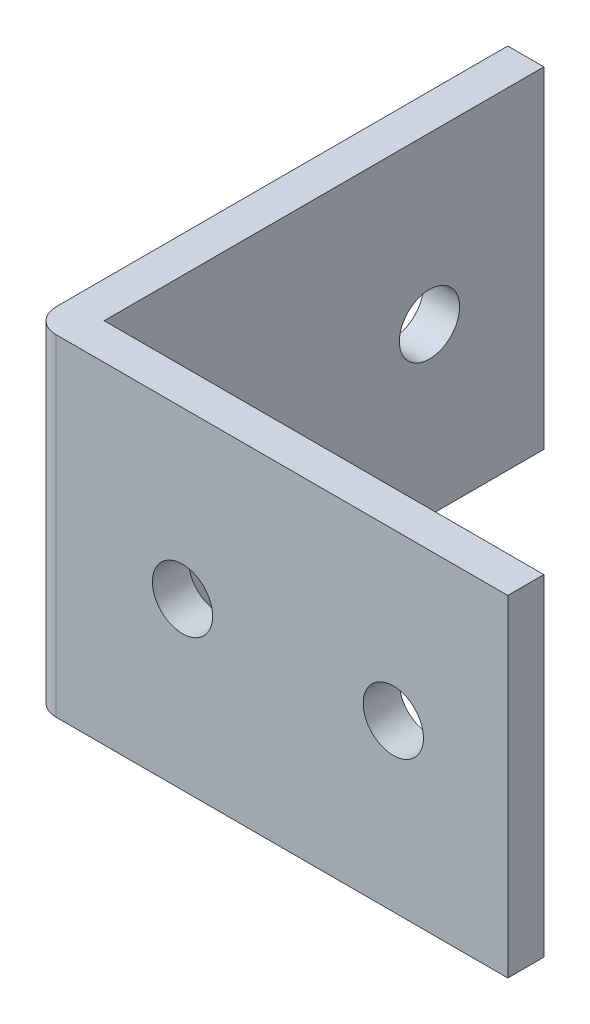
SolidWorks part; units mm, degrees
material "Stainless Steel (ferritic)"
ref_plane "Front Plane" through (0, 0, 0) normal (0, 0, 1) x (1, 0, 0)
ref_plane "Top Plane" through (0, 0, 0) normal (0, 1, 0) x (1, 0, 0)
ref_plane "Right Plane" through (0, 0, 0) normal (1, 0, 0) x (0, 0, -1)
sketch "Sketch1" plane through (0, 0, 0) normal (0, 0, 1) x (1, 0, 0)
  line L1 (-37.1328, 0.8528) -> (2.3672, 0.8528)
  line L2 (-37.1328, 0.8528) -> (-37.1328, -26.6472)
  line L3 (-37.1328, -26.6472) -> (2.3672, -26.6472)
  line L4 (2.3672, 0.8528) -> (2.3672, -26.6472)
  circle A0 centre (-24.6328, -12.8972) radius 2.5
  circle A1 centre (-7.1328, -12.8972) radius 2.5
  point P9 (2.3672, -12.8972)
  point P11 (-37.1328, -12.8972)
  dimension "D2" = 5
  dimension "D3" = 5
  dimension "D1" = 39.5
  dimension "D4" = 17.5
  dimension "D5" = 9.5
  dimension "D6" = 27.5
extrude "Boss-Extrude1" add sketch "Sketch1" along normal blind 3
sketch "Sketch3" plane through (0, 0, 0) normal (0, 0, -1) x (-1, 0, 0)
  line L0 (37.1328, -26.6472) -> (-2.3672, -26.6472) construction
  line L1 (37.1328, 0.8528) -> (34.1328, 0.8528)
  line L2 (37.1328, 0.8528) -> (37.1328, -26.6472)
  line L3 (37.1328, -26.6472) -> (34.1328, -26.6472)
  line L4 (34.1328, 0.8528) -> (34.1328, -26.6472)
  dimension "D1" = 3
extrude "Boss-Extrude2" add sketch "Sketch3" along normal blind 36.5
sketch "Sketch4" plane through (-34.1328, 0, 0) normal (1, 0, 0) x (0, 0, -1)
  line L1 (36.5, 0.8528) -> (36.5, -26.6472) construction
  circle A0 centre (9.5, -12.8972) radius 2.5
  circle A1 centre (27, -12.8972) radius 2.5
  point P8 (36.5, -12.8972)
  dimension "D3" = 5
  dimension "D1" = 17.5
  dimension "D2" = 9.5
extrude "Cut-Extrude1" cut sketch "Sketch4" against normal blind 36.5
fillet "Fillet1" radius 2 1 edges at (-37.1328, -12.8972, 3)
